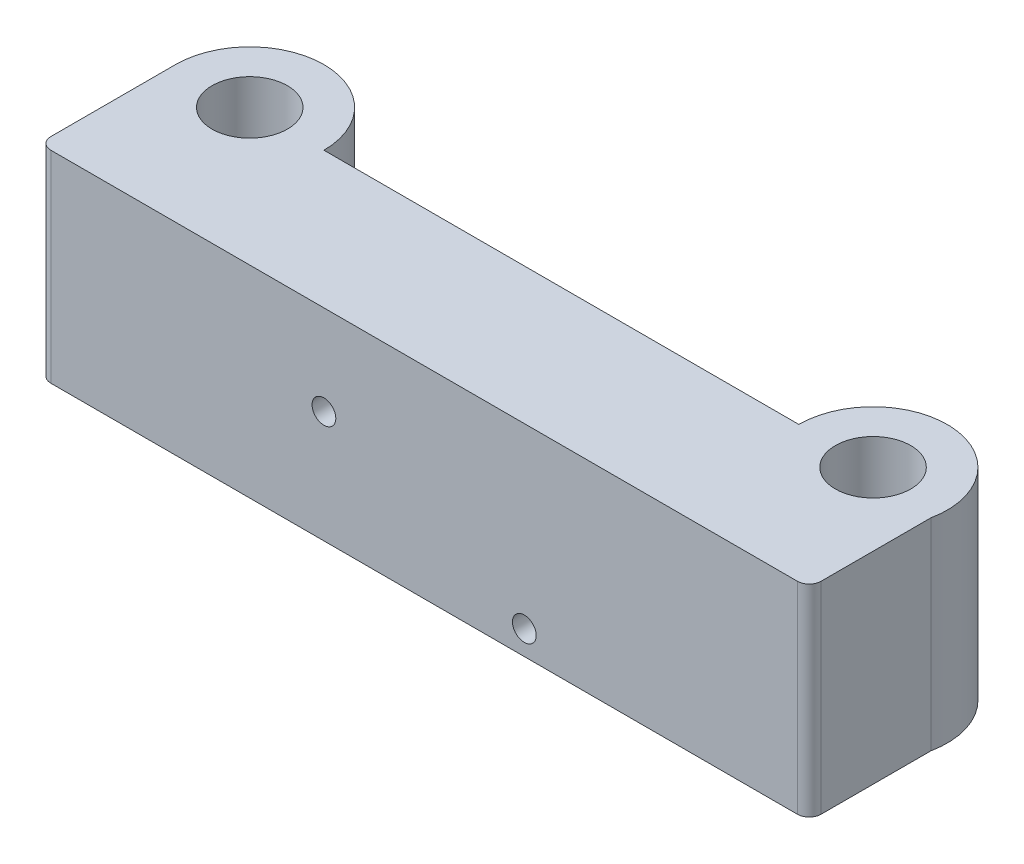
SolidWorks part; units mm, degrees
ref_plane "Front Plane" through (0, 0, 0) normal (0, 0, 1) x (1, 0, 0)
ref_plane "Top Plane" through (0, 0, 0) normal (0, 1, 0) x (1, 0, 0)
ref_plane "Right Plane" through (0, 0, 0) normal (1, 0, 0) x (0, 0, -1)
sketch "Sketch1" plane through (0, 0, 0) normal (0, 1, 0) x (1, 0, 0)
  line L1 (-24.9858, 0) -> (15.0205, 0)
  line L2 (-37.4858, 0) -> (-37.4858, -11.5)
  line L3 (-37.4858, -11.5) -> (27.3942, -11.5)
  line L4 (27.3942, -1.25) -> (27.3942, -11.5)
  arc A0 (-24.9858, 0) -> (-37.4858, 0) centre (-31.2358, 0) ccw
  arc A1 (27.3942, -1.25) -> (15.0205, 0) centre (21.2705, 0) ccw
  dimension "D1" = 12.5
  dimension "D2" = 12.5
  dimension "D3" = 11.5
  dimension "D4" = 64.88
extrude "Boss-Extrude1" add sketch "Sketch1" along normal blind 17
sketch "Sketch2" plane through (0, 17, 0) normal (0, 1, 0) x (1, 0, 0)
  circle A0 centre (-31.2358, 0) radius 3.175
  circle A1 centre (21.2705, 0) radius 3.175
  dimension "D1" = 6.35
  dimension "D2" = 6.35
extrude "Cut-Extrude1" cut sketch "Sketch2" against normal through all
sketch "Sketch4" plane through (0, 0, 11.5) normal (0, 0, 1) x (1, 0, 0)
  line L0 (-37.4858, 17) -> (-37.4858, 0) construction
  line L1 (27.3942, 17) -> (27.3942, 0) construction
  line L2 (-37.4858, 17) -> (27.3942, 17) construction
  circle A0 centre (-13.4858, 9.437) radius 1
  circle A1 centre (3.3942, 2.037) radius 1
  dimension "D1" = 2
  dimension "D2" = 2
  dimension "D5" = 14.963
  dimension "D3" = 24
  dimension "D4" = 24
  dimension "D6" = 7.563
extrude "Cut-Extrude3" cut sketch "Sketch4" against normal through all
fillet "Fillet1" radius 1 2 edges at (27.3942, 8.5, 11.5) (-37.4858, 8.5, 11.5)
